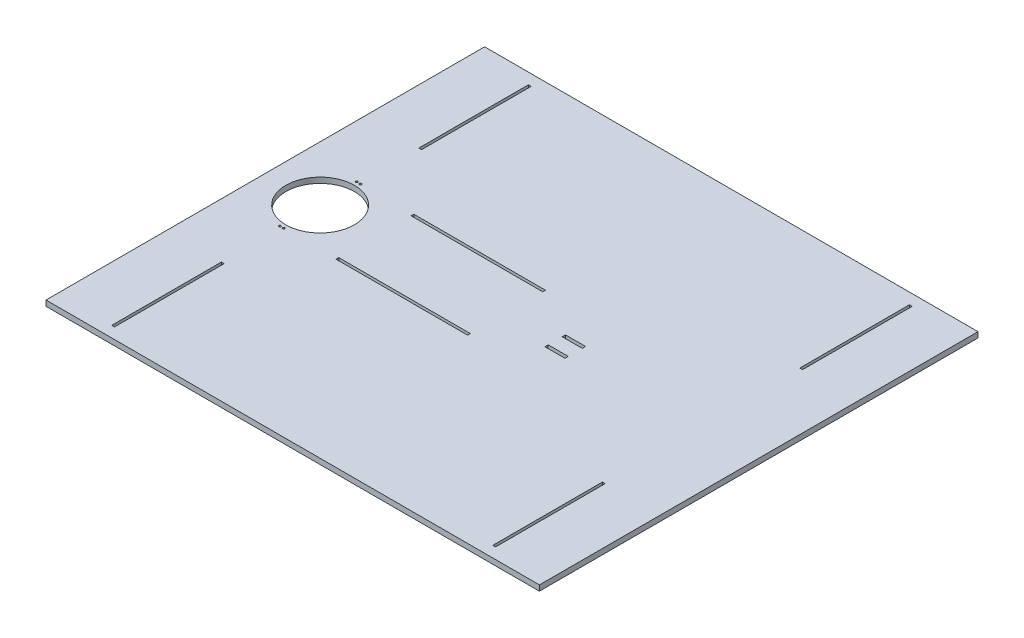
SolidWorks part; units mm, degrees
ref_plane "Front Plane" through (0, 0, 0) normal (0, 0, 1) x (1, 0, 0)
ref_plane "Top Plane" through (0, 0, 0) normal (0, 1, 0) x (1, 0, 0)
ref_plane "Right Plane" through (0, 0, 0) normal (1, 0, 0) x (0, 0, -1)
sketch "Sketch1" plane through (0, 0, 0) normal (0, 1, 0) x (1, 0, 0)
  line L0 (50, 300) -> (50, -500) construction
  line L1 (-400, 300) -> (500, 300)
  line L2 (-400, 300) -> (-400, -500)
  line L3 (-400, -500) -> (500, -500)
  line L4 (500, 300) -> (500, -500)
  line L5 (-400, -100) -> (500, -100) construction
  line L6 (400, 80) -> (395, 80)
  line L7 (-300, 280) -> (-295, 280)
  line L8 (-300, 280) -> (-300, 80)
  line L9 (-300, 80) -> (-295, 80)
  line L10 (-295, 280) -> (-295, 80)
  line L11 (395, 280) -> (395, 80)
  line L12 (400, 280) -> (395, 280)
  line L13 (400, 280) -> (400, 80)
  line L14 (-300, -280) -> (-295, -280)
  line L15 (-295, -480) -> (-295, -280)
  line L16 (-300, -480) -> (-295, -480)
  line L17 (-300, -480) -> (-300, -280)
  line L18 (400, -480) -> (400, -280)
  line L19 (400, -480) -> (395, -480)
  line L20 (395, -480) -> (395, -280)
  line L21 (400, -280) -> (395, -280)
  dimension "D1" = 800
  dimension "D2" = 900
  dimension "D3" = 500
  dimension "D4" = 500
  dimension "D5" = 5
  dimension "D6" = 200
  dimension "D7" = 100
  dimension "D8" = 20
extrude "Boss-Extrude1" add sketch "Sketch1" along normal blind 10
sketch "Sketch2" plane through (0, 0, 0) normal (0, 1, 0) x (1, 0, 0)
  line L0 (-400, -100) -> (500, -100) construction
  line L1 (-400, 300) -> (-400, -500) construction
  line L2 (500, -500) -> (500, 300) construction
  circle A0 centre (-300, -100) radius 62.5
  dimension "D1" = 125
  dimension "D2" = 100
extrude "Cut-Extrude4" cut sketch "Sketch2" along normal blind 196
sketch "Sketch3" plane through (0, 0, 0) normal (0, 1, 0) x (1, 0, 0)
  line L0 (-400, -100) -> (500, -100) construction
  line L1 (-400, 300) -> (-400, -500) construction
  line L2 (500, -500) -> (500, 300) construction
  line L3 (165.4071, -112.75) -> (165.4071, -118.75)
  line L4 (165.4071, -87.25) -> (128.8571, -87.25)
  line L5 (165.4071, -87.25) -> (165.4071, -81.25)
  line L6 (165.4071, -81.25) -> (128.8571, -81.25)
  line L7 (128.8571, -87.25) -> (128.8571, -81.25)
  line L8 (128.8571, -112.75) -> (128.8571, -118.75)
  line L9 (165.4071, -112.75) -> (128.8571, -112.75)
  line L10 (165.4071, -118.75) -> (128.8571, -118.75)
  line L11 (-237.5, -100) -> (-237.5, 74.6482) construction
  line L12 (-400, -166) -> (-400, -34) construction
  line L13 (-200, -166) -> (40, -166)
  line L14 (40, -166) -> (40, -171)
  line L15 (40, -171) -> (-200, -171)
  line L16 (-200, -171) -> (-200, -166)
  line L17 (-200, -29) -> (-200, -34)
  line L18 (40, -34) -> (40, -29)
  line L19 (40, -29) -> (-200, -29)
  line L20 (-200, -34) -> (40, -34)
  line L21 (-300, -37.5) -> (-300, -162.5) construction
  circle A0 centre (-300, -100) radius 62.5 construction
  circle A1 centre (-296.5, -30) radius 2
  circle A2 centre (-303.5, -30) radius 2
  circle A3 centre (-303.5, -170) radius 2
  circle A4 centre (-296.5, -170) radius 2
  point P20 (-400, -100)
  dimension "D9" = 4
  dimension "D1" = 36.55
  dimension "D2" = 6
  dimension "D3" = 12.75
  dimension "D4" = 366.3571
  dimension "D5" = 132
  dimension "D6" = 200
  dimension "D7" = 440
  dimension "D8" = 5
  dimension "D10" = 3.5
  dimension "D11" = 7.5
extrude "Cut-Extrude5" cut sketch "Sketch3" along normal through all contours L5 L4 L7 L6 | L3 L10 L8 L9 | L16 L13 L14 L15 | L17 L20 L18 L19 | A3 | A4 | A1 | A2
sketch "Sketch4" plane through (0, 10, 0) normal (0, 1, 0) x (1, 0, 0)
  line L0 (-400, -100) -> (500, -100) construction
  line L1 (-400, 300) -> (-285, 300)
  line L2 (-400, 300) -> (-400, 200)
  line L3 (-400, 200) -> (-285, 200)
  line L4 (-285, 300) -> (-285, 200)
  line L5 (-400, 300) -> (-400, -500) construction
  line L6 (500, -500) -> (500, 300) construction
  line L7 (50, 300) -> (50, -500) construction
  line L8 (500, 300) -> (-400, 300) construction
  line L9 (-400, -500) -> (500, -500) construction
  line L10 (-285, -500) -> (-285, -400)
  line L11 (-400, -400) -> (-285, -400)
  line L12 (-400, -500) -> (-400, -400)
  line L13 (-400, -500) -> (-285, -500)
  line L14 (500, -500) -> (385, -500)
  line L15 (500, -500) -> (500, -400)
  line L16 (500, -400) -> (385, -400)
  line L17 (385, -500) -> (385, -400)
  line L18 (385, 300) -> (385, 200)
  line L19 (500, 200) -> (385, 200)
  line L20 (500, 300) -> (500, 200)
  line L21 (500, 300) -> (385, 300)
  dimension "D1" = 670
  dimension "D2" = 600
extrude "Cut-Extrude6" [suppressed] cut sketch "Sketch4" against normal through all both and the other way through all
